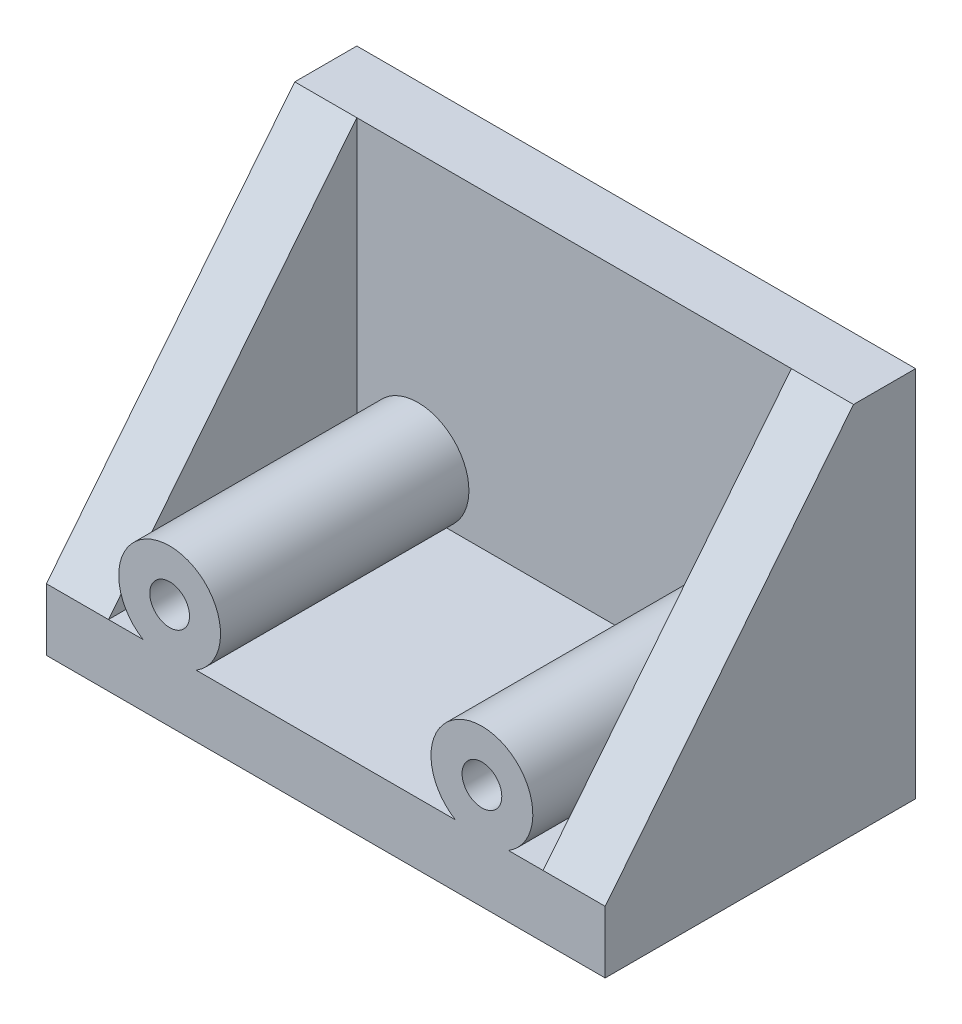
SolidWorks part; units mm, degrees
ref_plane "Front Plane" through (0, 0, 0) normal (0, 0, 1) x (1, 0, 0)
ref_plane "Top Plane" through (0, 0, 0) normal (0, 1, 0) x (1, 0, 0)
ref_plane "Right Plane" through (0, 0, 0) normal (1, 0, 0) x (0, 0, -1)
sketch "Sketch1" plane through (0, 0, 0) normal (0, 0, 1) x (1, 0, 0)
  line L1 (-90, 60) -> (90, 60)
  line L2 (-90, 60) -> (-90, -60)
  line L3 (-90, -60) -> (90, -60)
  line L4 (90, 60) -> (90, -60)
  line L5 (-90, 60) -> (90, -60) construction
  line L6 (-90, -60) -> (90, 60) construction
  point P0 (0, 0)
  dimension "D1" = 180
  dimension "D2" = 120
extrude "Boss-Extrude1" add sketch "Sketch1" along normal blind 20
sketch "Sketch4" plane through (0, -60, 0) normal (0, -1, 0) x (-1, 0, 0)
  line L0 (-90, -20) -> (-90, 0) construction
  line L1 (90, 0) -> (-90, 0)
  line L2 (90, 0) -> (90, -100)
  line L3 (90, -100) -> (-90, -100)
  line L4 (-90, 0) -> (-90, -100)
  dimension "D1" = 100
extrude "Boss-Extrude4" add sketch "Sketch4" against normal blind 20
sketch "Sketch5" plane through (90, 0, 0) normal (1, 0, 0) x (0, 0, -1)
  line L0 (-100, -40) -> (-20, -40)
  line L1 (-20, -40) -> (-20, 60)
  line L2 (-20, 60) -> (-100, -40)
extrude "Boss-Extrude5" add sketch "Sketch5" against normal blind 20
mirror "Mirror2" about plane through (0, 0, 0) normal (1, 0, 0) of "Boss-Extrude5"
sketch "Sketch6" plane through (0, 0, 20) normal (0, 0, 1) x (1, 0, 0)
  line L4 (90, -60) -> (-90, -60) construction
  line L5 (-41.7543, -40) -> (-58.8377, -40)
  line L6 (70, -40) -> (-70, -40) construction
  circle A0 centre (-50.296, -26) radius 6.4
  arc A1 (-41.7543, -40) -> (-58.8377, -40) centre (-50.296, -26) ccw
  dimension "D1" = 12.8
  dimension "D2" = 32.8
  dimension "D4" = 34
  dimension "D3" = 50.296
extrude "Boss-Extrude11" add sketch "Sketch6" along normal up to surface (80 mm away) up to face at (0, -46.6667, 100)
mirror "Mirror3" about plane through (0, 0, 0) normal (1, 0, 0) of "Boss-Extrude11"
